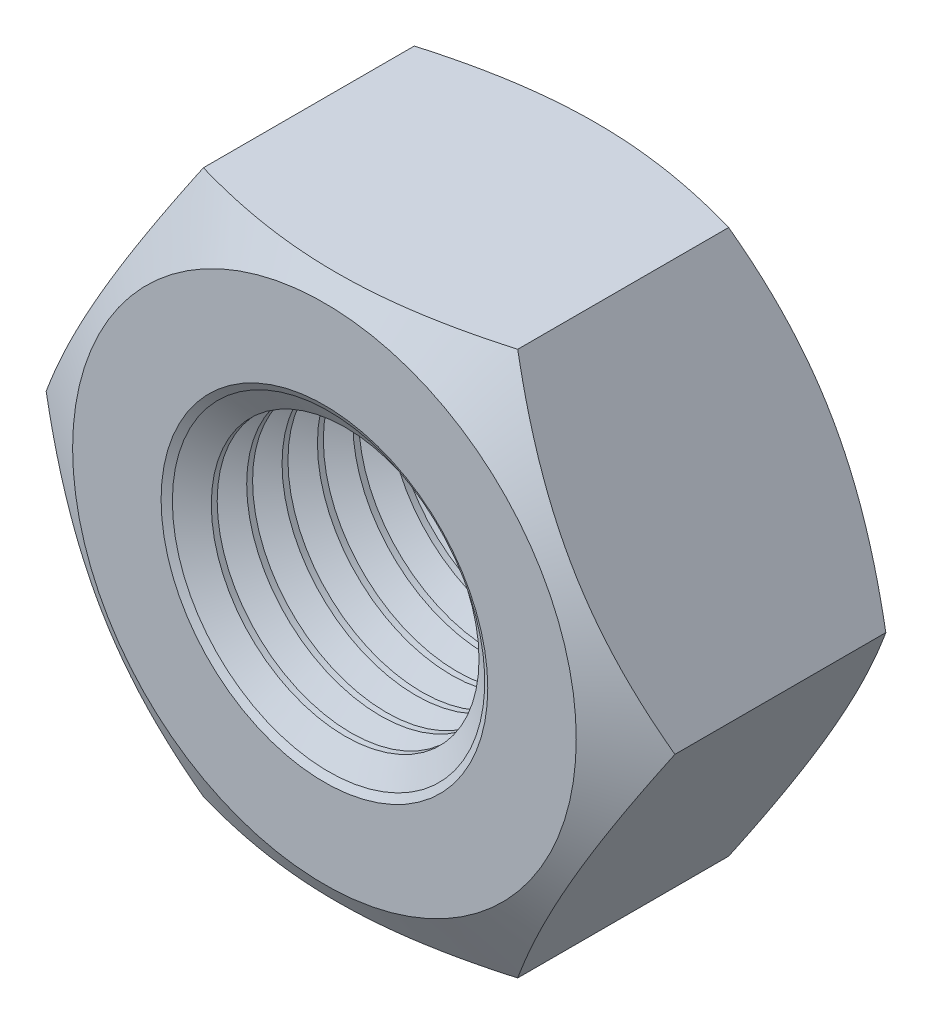
SolidWorks part; units mm, degrees
ref_plane "Front" through (0, 0, 0) normal (0, 0, 1) x (1, 0, 0)
ref_plane "Top" through (0, 0, 0) normal (0, 1, 0) x (1, 0, 0)
ref_plane "Right" through (0, 0, 0) normal (1, 0, 0) x (0, 0, -1)
sketch "Sketch1" plane through (0, 0, 0) normal (0, 0, 1) x (1, 0, 0)
  line L1 (5.7735, 0) -> (2.8868, 5)
  line L2 (2.8868, 5) -> (-2.8868, 5)
  line L3 (-2.8868, 5) -> (-5.7735, 0)
  line L4 (-5.7735, 0) -> (-2.8868, -5)
  line L5 (-2.8868, -5) -> (2.8868, -5)
  line L6 (2.8868, -5) -> (5.7735, 0)
  circle A0 centre (0, 0) radius 5 construction
  circle A1 centre (0, 0) radius 2.4585
  dimension "D" = 4.917
  dimension "s" = 10
extrude "BaseNut" add sketch "Sketch1" against normal blind 5.2
cosmetic thread "ThreadCosmetic1" [suppressed] parameters "D"=6
sketch "Sketch2" plane through (0, 0, 0) normal (0, 1, 0) x (1, 0, 0)
  line L0 (-5.7735, 5.2) -> (-4.625, 5.2)
  line L2 (-4.625, 5.2) -> (-5.7735, 4.5369)
  line L3 (-5.7735, 4.5369) -> (-5.7735, 5.2)
  line L4 (0, 3.3759) -> (0, -9.8171) construction
  line L6 (-9.7712, 2.6) -> (9.8853, 2.6) construction
  line L7 (-5.7735, 0.6631) -> (-5.7735, 0)
  line L8 (-4.625, 0) -> (-5.7735, 0.6631)
  line L9 (-5.7735, 0) -> (-4.625, 0)
  dimension "dw" = 9.25
  dimension "D1" = 30
  dimension "D2" = 2.6
revolve "Double-Chamfer" cut sketch "Sketch2" angle 360 about L4
chamfer "EndChamfer" distance 0.5415 angle 30 2 edges at (2.4585, 0, -5.2) (2.4585, 0, 0)
sketch "Sketch3" plane through (0, 0, 0) normal (0, 1, 0) x (1, 0, 0)
  line L0 (-2.9275, 4.6585) -> (-2.4585, 4.3877)
  line L1 (-2.4585, 4.3877) -> (-1.917, 4.3877)
  line L2 (-1.917, 4.3877) -> (-1.917, 4.9292)
  line L3 (-1.917, 4.9292) -> (-2.4585, 4.9292)
  line L4 (-2.4585, 4.9292) -> (-2.9275, 4.6585)
  line L5 (0, 7.4383) -> (0, 16.8806) construction
  dimension "D1" = 0.5415
  dimension "D2" = 4.917
revolve "Cut-Revolve10" cut sketch "Sketch3" angle 360 about L5
pattern_linear "LPattern10" count 8 spacing 0.6498 along (0, 0, 1) of "Cut-Revolve10"
equation "\"dw@Sketch2\" = \"s@Sketch1\"-0.75"
equation "\"D2@Sketch2\" = \"m@BaseNut\" / 2"
equation "\"D2@Sketch3\" = \"D@Sketch1\""
equation "\"D1@Sketch3\" =  (\"D@ThreadCosmetic1\"   - \"D@Sketch1\")  / 2"
equation "\"D3@LPattern10\" = \"D1@Sketch3\" * 1.2"
equation "\"D1@LPattern10\" = \"m@BaseNut\"/\"D3@LPattern10\""
